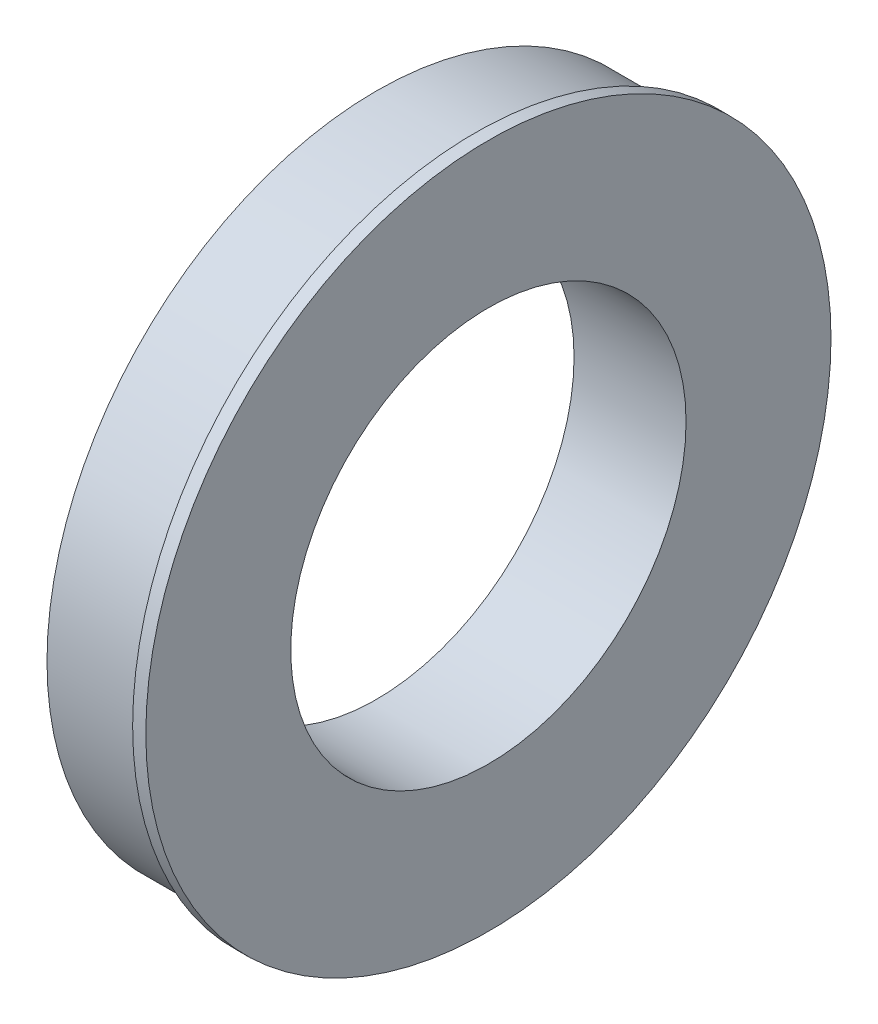
SolidWorks part; units mm, degrees
ref_plane "Front Plane" through (0, 0, 0) normal (0, 0, 1) x (1, 0, 0)
ref_plane "Top Plane" through (0, 0, 0) normal (0, 1, 0) x (1, 0, 0)
ref_plane "Right Plane" through (0, 0, 0) normal (1, 0, 0) x (0, 0, -1)
sketch "Sketch1" plane through (0, 0, 0) normal (1, 0, 0) x (0, 0, -1)
  circle A0 centre (0, 0) radius 38.1
  circle A1 centre (0, 0) radius 63.5
  dimension "D1" = 127
  dimension "D2" = 76.2
extrude "Boss-Extrude1" add sketch "Sketch1" along normal blind 19.05
sketch "Sketch3" plane through (19.05, 0, 0) normal (1, 0, 0) x (0, 0, -1)
  circle A1 centre (0, 0) radius 38.1 construction
  circle A2 centre (0, 0) radius 66.04
  circle A3 centre (0, 0) radius 66.04
  circle A4 centre (0, 0) radius 38.1
  dimension "D1" = 2.54
extrude "Boss-Extrude2" add sketch "Sketch3" along normal blind 2.54
